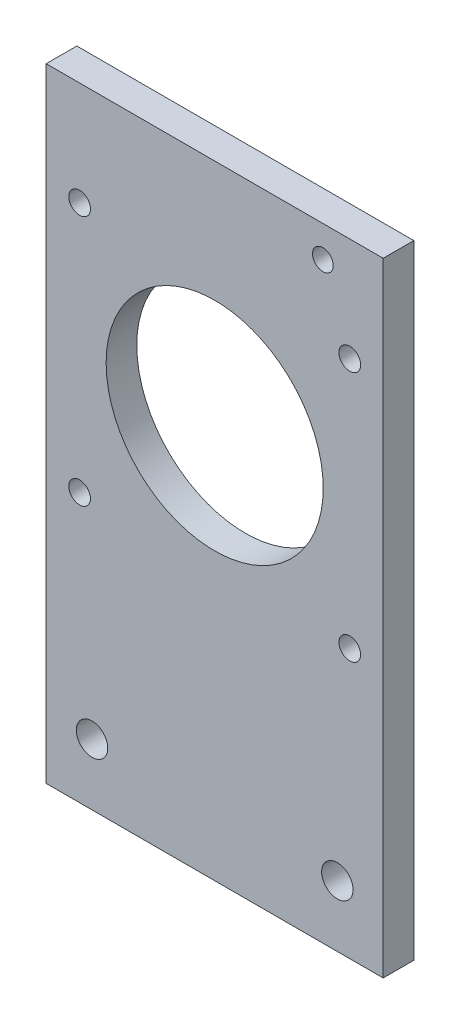
SolidWorks part; units mm, degrees
ref_plane "Front Plane" through (0, 0, 0) normal (0, 0, 1) x (1, 0, 0)
ref_plane "Top Plane" through (0, 0, 0) normal (0, 1, 0) x (1, 0, 0)
ref_plane "Right Plane" through (0, 0, 0) normal (1, 0, 0) x (0, 0, -1)
sketch "Sketch2" plane through (0, 0, 0) normal (0, 0, 1) x (1, 0, 0)
  line L0 (-55, 72.2) -> (55, 72.2) construction
  line L1 (-34.925, 0) -> (34.925, 0)
  line L2 (-34.925, 0) -> (-34.925, 81.7)
  line L3 (-34.925, 81.7) -> (34.925, 81.7) construction
  line L4 (34.925, 0) -> (34.925, 81.7)
  line L5 (0, 72.2) -> (0, 0) construction
  line L6 (0, 72.2) -> (0, 81.7) construction
  line L7 (-34.925, 25.4) -> (34.925, 25.4) construction
  line L10 (34.925, 114.2) -> (-34.925, 114.2) construction
  line L11 (34.925, 81.7) -> (34.925, 114.2)
  line L12 (34.925, 114.2) -> (-34.925, 114.2) construction
  line L13 (-34.925, 114.2) -> (-34.925, 81.7)
  line L14 (34.925, 114.2) -> (34.925, 129.2)
  line L15 (34.925, 129.2) -> (-34.925, 129.2)
  line L16 (-34.925, 114.2) -> (-34.925, 129.2)
  line L17 (-34.925, 25.4) -> (34.925, 25.4) construction
  circle A0 centre (-55, 72.2) radius 3 construction
  circle A1 centre (55, 72.2) radius 3 construction
  circle A2 centre (-55, 72.2) radius 15 construction
  circle A3 centre (55, 72.2) radius 15 construction
  circle A6 centre (0, 81.7) radius 22.5
  circle A7 centre (-55, 72.2) radius 15.6 construction
  point P6 (0, 0)
  dimension "D1" = 6
  dimension "D2" = 30
  dimension "D5" = 45
  dimension "D9" = 15
  dimension "D3" = 110
  dimension "D4" = 9.5
  dimension "D6" = 69.85
  dimension "D7" = 56.3
  dimension "D8" = 32.5
  dimension "D10" = 25.4
  dimension "D11" = 0.6
extrude "Boss-Extrude1" add sketch "Sketch2" along normal mid plane 6.35
sketch "Sketch3" plane through (0, 0, 3.175) normal (0, 0, 1) x (1, 0, 0)
  line L0 (34.925, 129.2) -> (-34.925, 129.2) construction
  line L1 (-34.925, 0) -> (-25.425, 0) construction
  line L2 (-34.925, 0) -> (-34.925, 12.7) construction
  line L3 (-34.925, 12.7) -> (-25.425, 12.7) construction
  line L4 (-25.425, 0) -> (-25.425, 12.7) construction
  line L5 (34.925, 0) -> (25.425, 0) construction
  line L6 (34.925, 0) -> (34.925, 12.7) construction
  line L7 (34.925, 12.7) -> (25.425, 12.7) construction
  line L8 (25.425, 0) -> (25.425, 12.7) construction
  line L10 (34.925, 0) -> (34.925, 129.2) construction
  circle A0 centre (-25.425, 12.7) radius 3.2576
  circle A1 centre (25.425, 12.7) radius 3.2576
  circle A2 centre (22.425, 122.7) radius 2.15
  dimension "D1" = 12.7
  dimension "D2" = 6.5151
  dimension "D4" = 4.3
  dimension "D5" = 6.5
  dimension "D3" = 9.5
  dimension "D6" = 12.5
extrude "Cut-Extrude1" cut sketch "Sketch3" against normal through all both and the other way through all
sketch "Sketch4" plane through (0, 0, -3.175) normal (0, 0, -1) x (-1, 0, 0)
  circle A0 centre (-28, 107.7) radius 2.25 construction
  circle A1 centre (28, 107.7) radius 2.25 construction
  circle A2 centre (-28, 55.7) radius 2.25 construction
  circle A3 centre (28, 55.7) radius 2.25 construction
  circle A4 centre (-28, 107.7) radius 2.25
  circle A5 centre (28, 107.7) radius 2.25
  circle A6 centre (-28, 55.7) radius 2.25
  circle A7 centre (28, 55.7) radius 2.25
extrude "Cut-Extrude2" cut sketch "Sketch4" against normal through all both and the other way through all
